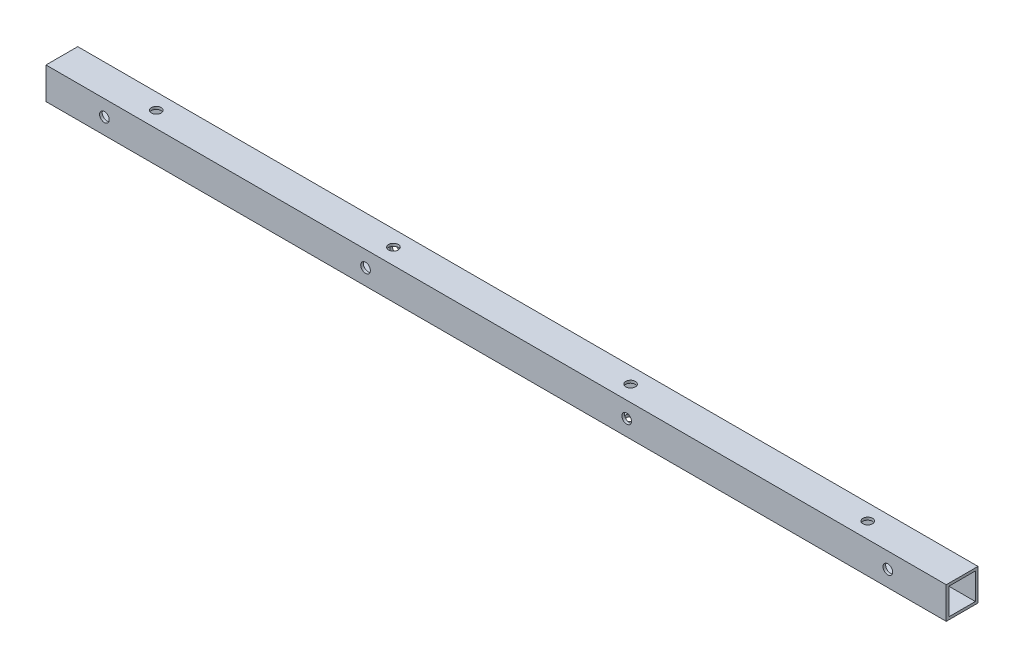
SolidWorks part; units mm, degrees
material "1060 Alloy"
ref_plane "Front Plane" through (0, 0, 0) normal (0, 0, 1) x (1, 0, 0)
ref_plane "Top Plane" through (0, 0, 0) normal (0, 1, 0) x (1, 0, 0)
ref_plane "Right Plane" through (0, 0, 0) normal (1, 0, 0) x (0, 0, -1)
sketch "Sketch1" plane through (0, 0, 0) normal (1, 0, 0) x (0, -1, 0)
  line L1 (-9.525, 9.525) -> (9.525, 9.525)
  line L2 (-9.525, 9.525) -> (-9.525, -9.525)
  line L3 (-9.525, -9.525) -> (9.525, -9.525)
  line L4 (9.525, 9.525) -> (9.525, -9.525)
  line L5 (-9.525, 9.525) -> (9.525, -9.525) construction
  line L6 (-9.525, -9.525) -> (9.525, 9.525) construction
  line L7 (-7.9375, 7.9375) -> (7.9375, 7.9375)
  line L8 (-7.9375, 7.9375) -> (-7.9375, -7.9375)
  line L9 (-7.9375, -7.9375) -> (7.9375, -7.9375)
  line L10 (7.9375, 7.9375) -> (7.9375, -7.9375)
  line L11 (-7.9375, 7.9375) -> (7.9375, -7.9375) construction
  line L12 (-7.9375, -7.9375) -> (7.9375, 7.9375) construction
  point P0 (0, 0)
  point P5 (0, 0)
  dimension "D2" = 19.05
  dimension "D1" = 15.875
extrude "Tube" add sketch "Sketch1" along normal blind 539.9532
sketch "Sketch2" plane through (0, 0, 9.525) normal (0, 0, 1) x (1, 0, 0)
  line L0 (504.9266, 0) -> (539.9532, 0) construction
  line L1 (539.9532, 9.525) -> (539.9532, -9.525) construction
  line L2 (539.9532, 0) -> (559.0032, 0) construction
  line L4 (559.0032, 0) -> (562.0766, 0) construction
  circle A2 centre (504.9266, 0) radius 2.8956
  dimension "D1" = 5.7912
  dimension "D2" = 19.05
  dimension "D3" = 3.0734
  dimension "D4" = 57.15
extrude "RearWallHoles" cut sketch "Sketch2" against normal through all
pattern_linear "LPattern1" count 4 spacing 156.6333 along (-1, 0, 0) of "RearWallHoles"
sketch "Sketch3" plane through (0, 9.525, 0) normal (0, 1, 0) x (1, 0, 0)
  line L0 (0, 0) -> (-19.05, 0) construction
  line L1 (-19.05, 0) -> (-22.1234, 0) construction
  line L2 (0, 0) -> (56.6166, 0) construction
  circle A0 centre (56.6166, 0) radius 2.8956
  dimension "D1" = 5.7912
  dimension "D2" = 3.0734
  dimension "D3" = 19.05
  dimension "D4" = 78.74
extrude "RearTopHoleMaster" cut sketch "Sketch3" against normal through all
pattern_linear "LPattern2" count 4 spacing 142.24 along (1, 0, 0) of "RearTopHoleMaster"
equation "\"Height\"= 32in"
equation "\"Width\"= 23in"
equation "\"Depth\"= 20in"
equation "\"Plexi\"= .121in"
equation "\"Cutwidth\"= .016in"
equation "\"Earsize\"= 1in + \"Cutwidth\" /2"
equation "\"Slotsize\" = 1in - \"CutWidth\" / 2"
equation "\"InnerHeight\" = \"Height\" -2 * \"Plexi\""
equation "\"InnerWidth\" = \"Width\" - 2* \"Plexi\""
equation "\"RearHoleSpacing\" = (\"Width\" - 2*\"RearHolesBorder\") / (\"RearNumHoles\"-1)"
equation "\"D4@Sketch2\"=\"RearHolesBorder\""
equation "\"Boxsize\" = .75in"
equation "\"Boxinner\" = .625in"
equation "\"InnerDepth\" = \"Depth\" - 2*\"Plexi\""
equation "\"RearNumHoles\" = 4"
equation "\"RearHolesBorder\" = 2.25"
equation "\"SideVertNumHoles\" = 4"
equation "\"SideVertHolesBorder\" = \"CornerCube\"+\"FingerLength\"+1.50"
equation "\"RivetDia\" = .228in"
equation "\"SlotDepth\" = \"Plexi\" + 0.75in + .005in"
equation "\"SideSlotWidth\"   = \"Plexi\"+.005in"
equation "\"SidePanelVertSpacing\" = (\"Height\"-2*(1.75-\"Plexi\")) / 5"
equation "\"BottomPanelSideHoleSpacing\" = (\"InnerDepth\"-2*(1.75-\"Plexi\")) / 4"
equation "\"D2@Sketch1\"=\"Boxsize\""
equation "\"D1@Sketch1\"=\"Boxinner\""
equation "\"CornerCube\" = 0.75in"
equation "\"RearBarLength\" = (\"InnerWidth\"-2*\"CornerCube\")"
equation "\"D1@Sketch2\"=\"RivetDia\""
equation "\"D2@Sketch2\"=\"CornerCube\""
equation "\"D3@Sketch2\"=\"Plexi\""
equation "\"D3@LPattern1\"=\"RearHoleSpacing\""
equation "\"D1@LPattern1\"=\"RearNumHoles\""
equation "\"D1@Tube\"=\"RearBarLength\""
equation "\"D1@Sketch3\"=\"RivetDia\""
equation "\"D2@Sketch3\"=\"Plexi\""
equation "\"D3@Sketch3\"=\"CornerCube\""
equation "\"RearTopNumHoles\" = 4"
equation "\"RearTopHolesBorder\" = 3.1"
equation "\"RearTopHolesSpacing\" = (\"Width\" - 2*\"RearTopHolesBorder\") / (\"RearTopNumHoles\"-1)"
equation "\"SideVertHoleSpacing\" = (\"SideVertBarLength\" - 2*(\"SideVertHolesBorder\"-\"Plexi\"-\"CornerCube\")) / (\"SideVertNumHoles\"-1)"
equation "\"D4@Sketch3\"=\"RearTopHolesBorder\""
equation "\"D3@LPattern2\"=\"RearTopHolesSpacing\""
equation "\"D1@LPattern2\"=\"RearTopNumHoles\""
